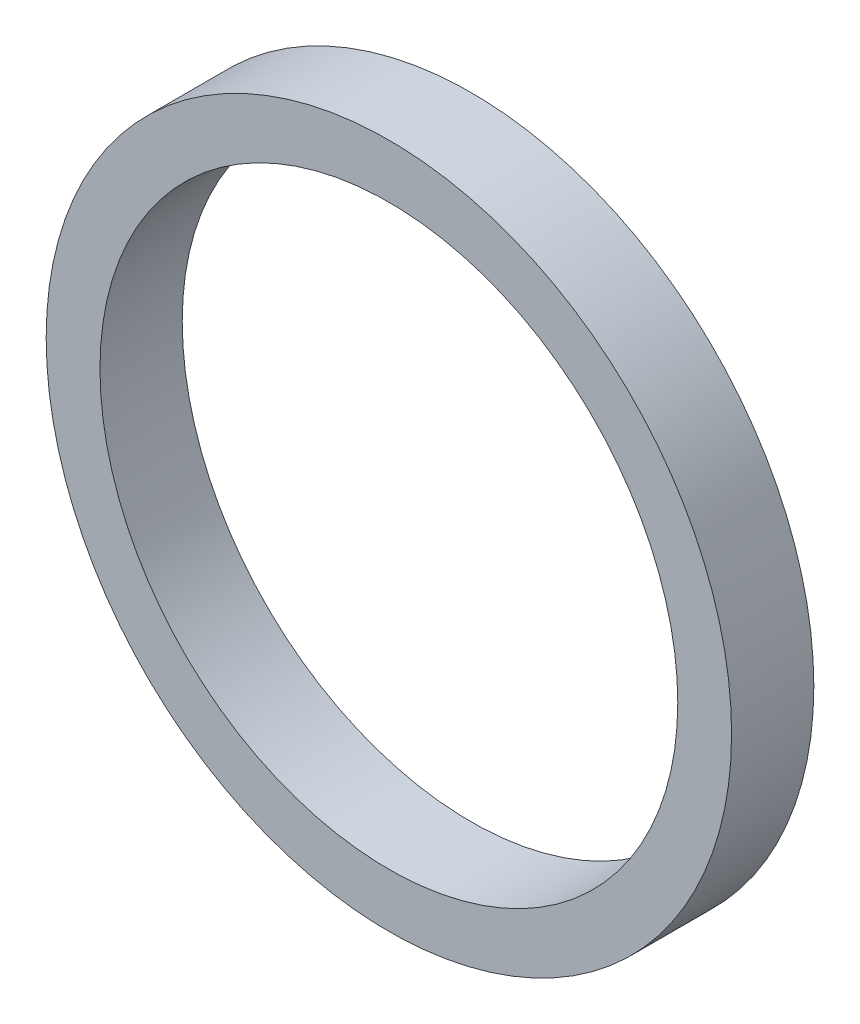
SolidWorks part; units mm, degrees
ref_plane "Front Plane" through (0, 0, 0) normal (0, 0, 1) x (1, 0, 0)
ref_plane "Top Plane" through (0, 0, 0) normal (0, 1, 0) x (1, 0, 0)
ref_plane "Right Plane" through (0, 0, 0) normal (1, 0, 0) x (0, 0, -1)
sketch "Sketch1" plane through (0, 0, 0) normal (0, 0, 1) x (1, 0, 0)
  circle A0 centre (0, 0) radius 25
  dimension "D1" = 50
extrude "Boss-Extrude1" add sketch "Sketch1" along normal blind 6
sketch "Sketch2" plane through (0, 0, 0) normal (0, 0, -1) x (-1, 0, 0)
  circle A0 centre (0, 0) radius 21.075
  dimension "D1" = 42.15
extrude "Cut-Extrude1" cut sketch "Sketch2" against normal through all
